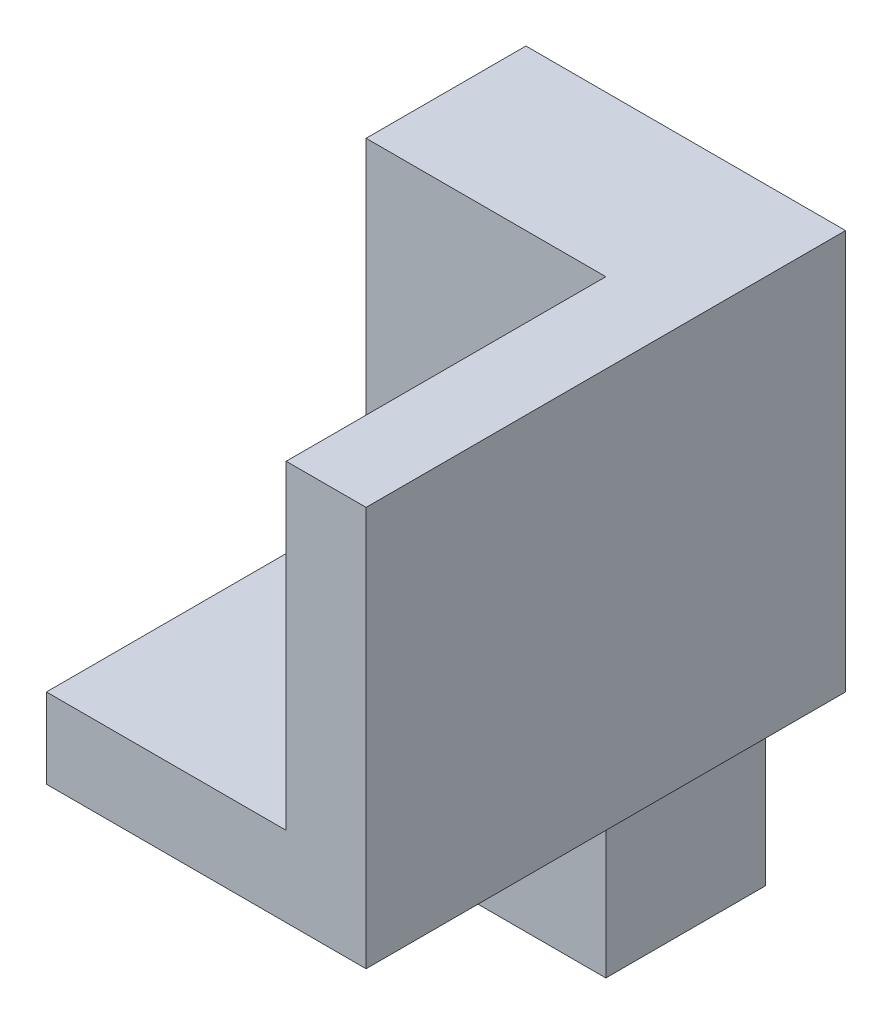
SolidWorks part; units mm, degrees
ref_plane "Front Plane" through (0, 0, 0) normal (0, 0, 1) x (1, 0, 0)
ref_plane "Top Plane" through (0, 0, 0) normal (0, 1, 0) x (1, 0, 0)
ref_plane "Right Plane" through (0, 0, 0) normal (1, 0, 0) x (0, 0, -1)
sketch "Sketch1" plane through (0, 0, 0) normal (1, 0, 0) x (0, 0, -1)
  line L0 (0, -1509.5556) -> (0, 73968.222) construction
  line L1 (0, 0) -> (-10, 0)
  line L2 (-10, 0) -> (-10, -20)
  line L3 (-10, -20) -> (-30, -20)
  line L6 (0, -38) -> (0, 0)
  line L7 (-30, -20) -> (-30, -25)
  line L8 (-30, -25) -> (-10, -25)
  line L9 (-10, -25) -> (-10, -38)
  line L10 (-10, -38) -> (0, -38)
  dimension "D1" = 20
  dimension "D2" = 20
  dimension "D3" = 5
  dimension "D4" = 10
  dimension "D5" = 10
  dimension "D6" = 38
extrude "Boss-Extrude1" add sketch "Sketch1" along normal blind 10
sketch "Sketch2" plane through (0, 0, 0) normal (-1, 0, 0) x (0, 0, 1)
  line L0 (0, 0) -> (10, 0)
  line L1 (10, 0) -> (10, -20)
  line L2 (10, -20) -> (30, -20)
  line L3 (30, -20) -> (30, -25)
  line L4 (30, -25) -> (0, -25)
  line L5 (0, -38) -> (0, 0) construction
  line L6 (0, -25) -> (0, 0)
extrude "Boss-Extrude5" add sketch "Sketch2" along normal blind 5
sketch "Sketch3" plane through (10, 0, 0) normal (1, 0, 0) x (0, 0, -1)
  line L1 (0, 0) -> (-30, 0)
  line L2 (0, 0) -> (0, -25)
  line L3 (0, -25) -> (-30, -25)
  line L4 (-30, 0) -> (-30, -25)
extrude "Boss-Extrude6" add sketch "Sketch3" along normal blind 5
